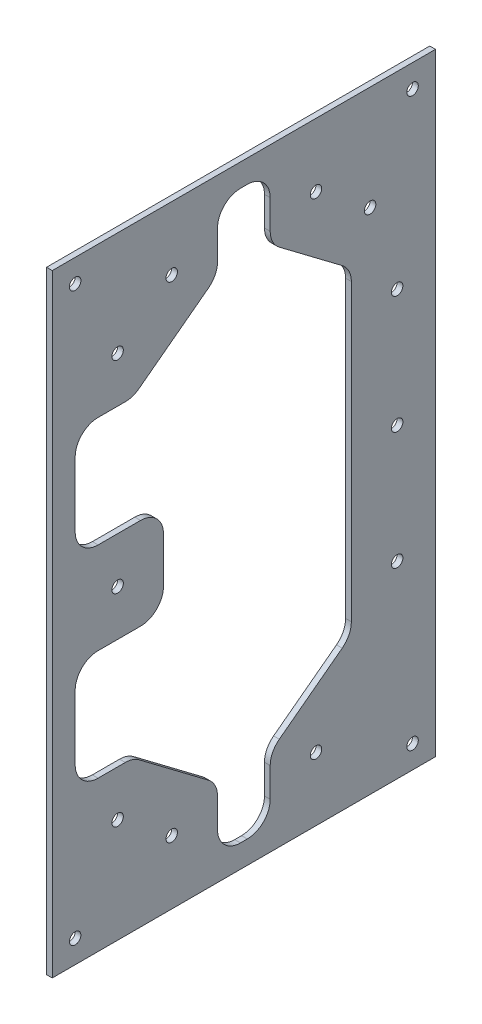
SolidWorks part; units mm, degrees
material "6061-T6 (SS)"
ref_plane "Front Plane" through (0, 0, 0) normal (0, 0, 1) x (1, 0, 0)
ref_plane "Top Plane" through (0, 0, 0) normal (0, 1, 0) x (1, 0, 0)
ref_plane "Right Plane" through (0, 0, 0) normal (1, 0, 0) x (0, 0, -1)
sketch "Sketch1" plane through (0, 0, 0) normal (1, 0, 0) x (0, 0, -1)
  line L0 (0, -169.8625) -> (212.5, -169.8625) construction
  line L1 (0, 0) -> (212.5, 0)
  line L2 (0, 0) -> (0, -339.725)
  line L3 (0, -339.725) -> (212.5, -339.725)
  line L4 (212.5, 0) -> (212.5, -339.725)
  line L5 (153.5, -35.2425) -> (59, -35.2425) construction
  line L6 (191.25, -104.5325) -> (191.25, -169.8625) construction
  line L7 (13.5, -50.2425) -> (59, -50.2425) construction
  line L8 (36.25, -50.2425) -> (36.25, -169.8625) construction
  line L9 (106.25, 0) -> (106.25, -339.725) construction
  line L10 (173.5, -104.5325) -> (191.25, -104.5325) construction
  circle A0 centre (12.7, -12.7) radius 3.175
  circle A1 centre (199.8, -12.7) radius 3.175
  circle A2 centre (66.25, -35.2425) radius 3.175
  circle A3 centre (146.25, -35.2425) radius 3.175
  circle A4 centre (176.25, -57.8625) radius 3.175
  circle A5 centre (36.25, -57.8625) radius 3.175
  circle A6 centre (191.25, -104.5325) radius 3.175
  circle A7 centre (36.25, -169.8625) radius 3.175
  circle A8 centre (191.25, -169.8625) radius 3.175
  circle A9 centre (36.25, -281.8625) radius 3.175
  circle A10 centre (66.25, -304.4825) radius 3.175
  circle A11 centre (12.7, -327.025) radius 3.175
  circle A12 centre (199.8, -327.025) radius 3.175
  circle A13 centre (146.25, -304.4825) radius 3.175
  circle A14 centre (191.25, -235.1925) radius 3.175
  point P45 (0, 0)
  point P46 (0, 0)
  dimension "D1" = 339.725
  dimension "D2" = 212.5
  dimension "D3" = 40
  dimension "D4" = 112
  dimension "D5" = 85
  dimension "D6" = 157.1625
extrude "Boss-Extrude1" add sketch "Sketch1" along normal blind 3.175
sketch "Sketch2" plane through (3.175, 0, 0) normal (1, 0, 0) x (0, 0, -1)
  line L1 (165.85, -88.1617) -> (165.85, -251.5633)
  line L4 (0, 0) -> (0, -339.725)
  line L5 (0, -339.725) -> (212.5, -339.725)
  line L6 (212.5, -339.725) -> (212.5, 0)
  line L7 (212.5, 0) -> (0, 0)
  line L8 (0, 0) -> (0, -339.725)
  line L9 (0, -339.725) -> (212.5, -339.725)
  line L10 (212.5, -339.725) -> (212.5, 0)
  line L11 (212.5, 0) -> (0, 0)
  line L14 (25.4, -144.4625) -> (48.95, -144.4625)
  line L15 (25.4, -83.2625) -> (40.5014, -83.2625)
  line L16 (12.7, -95.9625) -> (12.7, -131.7625)
  line L17 (34.7163, -60.6425) -> (37.7837, -60.6425)
  line L18 (61.65, -70.5625) -> (61.65, -70.522)
  line L19 (61.65, -182.5625) -> (61.65, -157.1625)
  line L20 (36.25, -57.8625) -> (66.25, -35.2425) construction
  line L21 (48.1473, -80.703) -> (86.5959, -51.7127)
  line L22 (91.65, -25.4) -> (91.65, -41.5722)
  line L23 (120.85, -25.4) -> (120.85, -41.5722)
  line L24 (104.35, -12.7) -> (108.15, -12.7)
  line L25 (176.25, -57.8625) -> (146.25, -35.2425) construction
  line L26 (125.9041, -51.7127) -> (160.7959, -78.0212)
  line L27 (0, -169.8625) -> (212.5, -169.8625) construction
  line L28 (176.25, -281.8625) -> (146.25, -304.4825) construction
  line L29 (36.25, -281.8625) -> (66.25, -304.4825) construction
  line L30 (125.9041, -288.0123) -> (160.7959, -261.7038)
  line L31 (104.35, -327.025) -> (108.15, -327.025)
  line L32 (120.85, -314.325) -> (120.85, -298.1528)
  line L33 (91.65, -314.325) -> (91.65, -298.1528)
  line L34 (48.1473, -259.022) -> (86.5959, -288.0123)
  line L35 (61.65, -269.1625) -> (61.65, -269.203)
  line L36 (34.7163, -279.0825) -> (37.7837, -279.0825)
  line L37 (12.7, -243.7625) -> (12.7, -207.9625)
  line L38 (25.4, -256.4625) -> (40.5014, -256.4625)
  line L39 (25.4, -195.2625) -> (48.95, -195.2625)
  circle A0 centre (176.25, -57.8625) radius 3.175 construction
  circle A1 centre (146.25, -35.2425) radius 3.175 construction
  circle A2 centre (66.25, -35.2425) radius 3.175 construction
  circle A3 centre (36.25, -57.8625) radius 3.175 construction
  circle A4 centre (36.25, -169.8625) radius 3.175 construction
  circle A5 centre (36.25, -281.8625) radius 3.175 construction
  circle A6 centre (66.25, -304.4825) radius 3.175 construction
  circle A7 centre (146.25, -304.4825) radius 3.175 construction
  circle A8 centre (191.25, -235.1925) radius 3.175 construction
  circle A9 centre (191.25, -169.8625) radius 3.175 construction
  circle A10 centre (191.25, -104.5325) radius 3.175 construction
  circle A11 centre (176.25, -57.8625) radius 3.175 construction
  circle A12 centre (146.25, -35.2425) radius 3.175 construction
  circle A13 centre (66.25, -35.2425) radius 3.175 construction
  circle A14 centre (36.25, -57.8625) radius 3.175 construction
  circle A15 centre (36.25, -169.8625) radius 3.175 construction
  circle A16 centre (36.25, -281.8625) radius 3.175 construction
  circle A17 centre (66.25, -304.4825) radius 3.175 construction
  circle A18 centre (146.25, -304.4825) radius 3.175 construction
  circle A19 centre (191.25, -235.1925) radius 3.175 construction
  circle A20 centre (191.25, -169.8625) radius 3.175 construction
  circle A21 centre (191.25, -104.5325) radius 3.175 construction
  arc A28 (48.95, -144.4625) -> (61.65, -157.1625) centre (48.95, -157.1625) cw
  arc A29 (12.7, -131.7625) -> (25.4, -144.4625) centre (25.4, -131.7625) ccw
  arc A30 (12.7, -95.9625) -> (25.4, -83.2625) centre (25.4, -95.9625) cw
  arc A33 (165.85, -88.1617) -> (160.7959, -78.0212) centre (153.15, -88.1617) ccw
  arc A34 (125.9041, -51.7127) -> (120.85, -41.5722) centre (133.55, -41.5722) cw
  arc A35 (108.15, -12.7) -> (120.85, -25.4) centre (108.15, -25.4) cw
  arc A36 (104.35, -12.7) -> (91.65, -25.4) centre (104.35, -25.4) ccw
  arc A37 (86.5959, -51.7127) -> (91.65, -41.5722) centre (78.95, -41.5722) ccw
  arc A38 (48.1473, -80.703) -> (40.5014, -83.2625) centre (40.5014, -70.5625) cw
  circle A39 centre (36.25, -281.8625) radius 3.175 construction
  circle A40 centre (66.25, -304.4825) radius 3.175 construction
  circle A41 centre (146.25, -304.4825) radius 3.175 construction
  circle A42 centre (176.25, -281.8625) radius 3.175 construction
  arc A43 (48.1473, -259.022) -> (40.5014, -256.4625) centre (40.5014, -269.1625) ccw
  arc A44 (86.5959, -288.0123) -> (91.65, -298.1528) centre (78.95, -298.1528) cw
  arc A45 (104.35, -327.025) -> (91.65, -314.325) centre (104.35, -314.325) cw
  arc A46 (108.15, -327.025) -> (120.85, -314.325) centre (108.15, -314.325) ccw
  arc A47 (125.9041, -288.0123) -> (120.85, -298.1528) centre (133.55, -298.1528) ccw
  arc A48 (165.85, -251.5633) -> (160.7959, -261.7038) centre (153.15, -251.5633) cw
  arc A49 (12.7, -243.7625) -> (25.4, -256.4625) centre (25.4, -243.7625) ccw
  arc A50 (12.7, -207.9625) -> (25.4, -195.2625) centre (25.4, -207.9625) cw
  arc A51 (48.95, -195.2625) -> (61.65, -182.5625) centre (48.95, -182.5625) ccw
  point P46 (0, 0)
  point P73 (61.65, -83.2625)
  point P78 (61.65, -60.6425)
  point P92 (61.65, -279.0825)
  point P110 (61.65, -169.8625)
  point P114 (165.85, -169.8625)
  point P115 (61.65, -256.4625)
  dimension "D11" = 25.4
  dimension "D13" = 25.4
  dimension "D17" = 12.7
  dimension "D2" = 25.4
  dimension "D7" = 25.4
  dimension "D8" = 25.4
  dimension "D9" = 25.4
  dimension "D14" = 25.4
  dimension "D15" = 12.7
  dimension "D16" = 25.4
  dimension "D1" = 0
extrude "Cut-Extrude1" cut sketch "Sketch2" against normal through all
